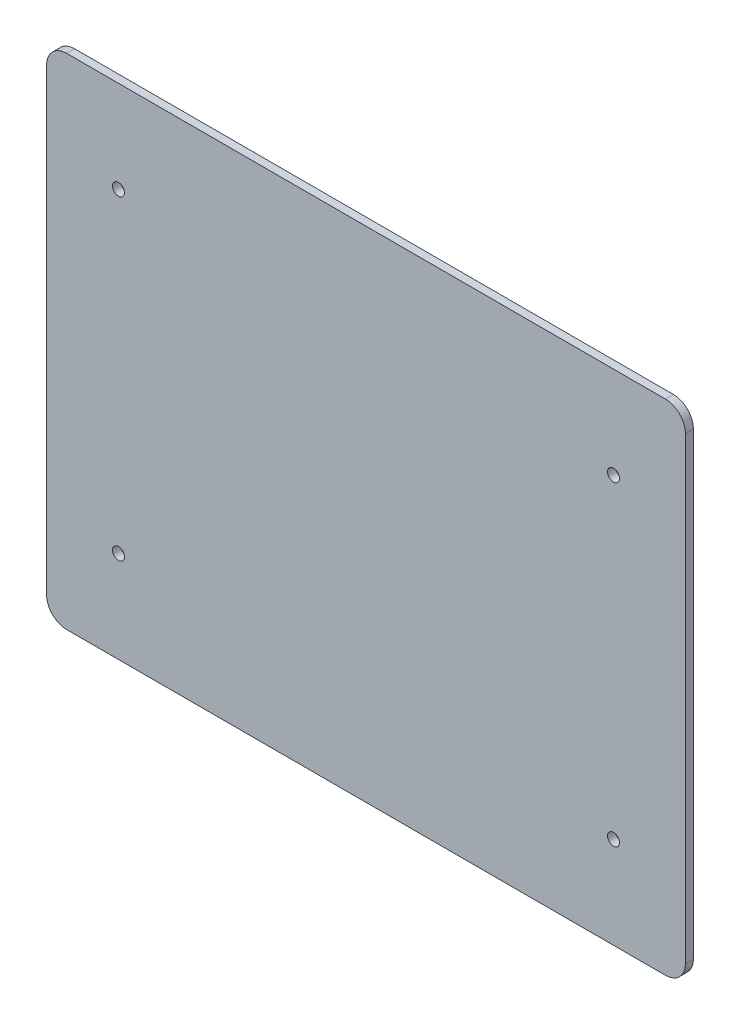
SolidWorks part; units mm, degrees
material "Cobre"
ref_plane "Plano frontal" through (0, 0, 0) normal (0, 0, 1) x (1, 0, 0)
ref_plane "Plano superior" through (0, 0, 0) normal (0, 1, 0) x (1, 0, 0)
ref_plane "Plano direito" through (0, 0, 0) normal (1, 0, 0) x (0, 0, -1)
sketch "Esboço1" plane through (0, 0, 0) normal (0, 0, 1) x (1, 0, 0)
  line L1 (47.3676, -148.0271) -> (-102.6324, -148.0271)
  line L2 (52.3676, -143.0271) -> (52.3676, -28.0271)
  line L3 (47.3676, -23.0271) -> (-102.6324, -23.0271)
  line L4 (-107.6324, -143.0271) -> (-107.6324, -28.0271)
  arc A0 (-102.6324, -148.0271) -> (-107.6324, -143.0271) centre (-102.6324, -143.0271) cw
  arc A1 (-102.6324, -23.0271) -> (-107.6324, -28.0271) centre (-102.6324, -28.0271) ccw
  arc A2 (52.3676, -28.0271) -> (47.3676, -23.0271) centre (47.3676, -28.0271) ccw
  arc A3 (47.3676, -148.0271) -> (52.3676, -143.0271) centre (47.3676, -143.0271) ccw
  point P6 (-107.6324, -148.0271)
  point P9 (-107.6324, -23.0271)
  point P14 (52.3676, -148.0271)
  dimension "D3" = 5
  dimension "D1" = 160
  dimension "D2" = 125
extrude "Ressalto-extrusão1" add sketch "Esboço1" along normal blind 2
sketch "Esboço2" plane through (0, 0, 0) normal (0, 0, -1) x (-1, 0, 0)
  line L0 (27.6324, -148.0271) -> (27.6324, -116.7121) construction
  line L2 (102.6324, -148.0271) -> (-47.3676, -148.0271) construction
  line L4 (-52.3676, -143.0271) -> (-52.3676, -28.0271) construction
  circle A0 centre (-34.3676, -125.0271) radius 1.5
  circle A2 centre (-34.3676, -46.0271) radius 1.5
  circle A3 centre (89.6324, -46.0271) radius 1.5
  circle A5 centre (89.6324, -125.0271) radius 1.5
  dimension "D1" = 79
  dimension "D5" = 3
  dimension "D6" = 3
  dimension "D7" = 23
  dimension "D8" = 18
  dimension "D9" = 18
extrude "Corte-extrusão1" cut sketch "Esboço2" against normal blind 10
